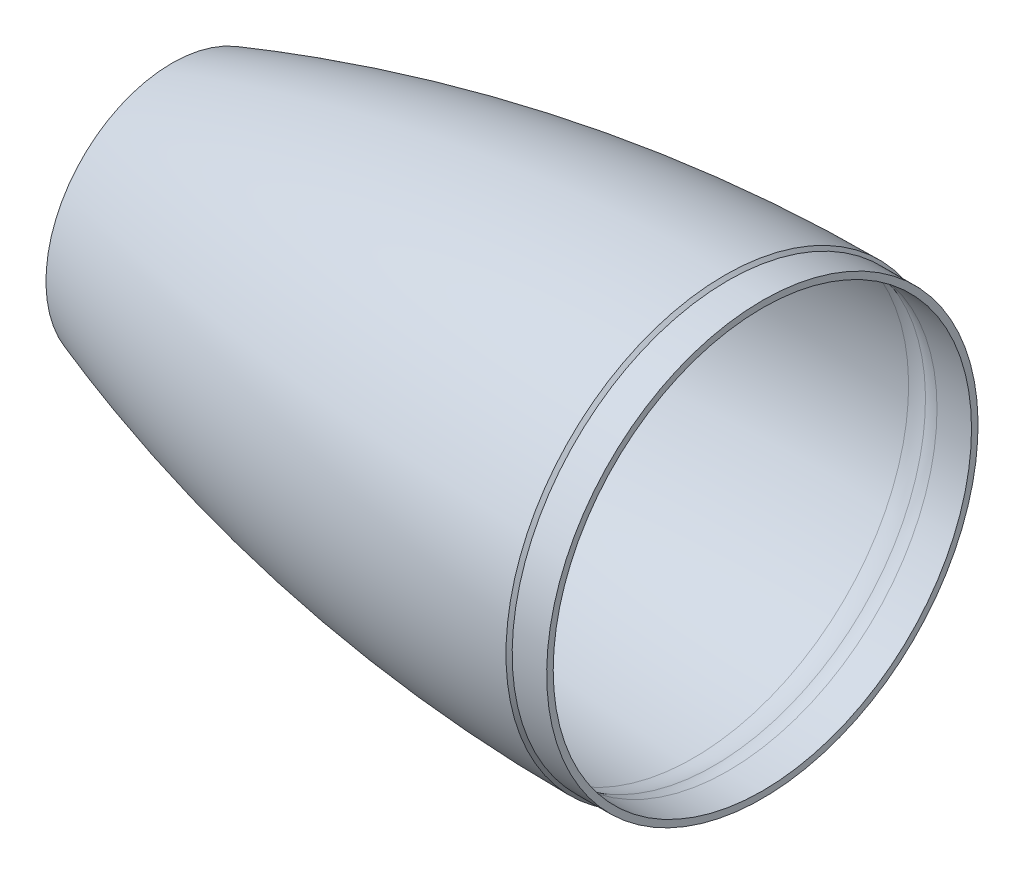
SolidWorks part; units mm, degrees
ref_plane "Front Plane" through (0, 0, 0) normal (0, 0, 1) x (1, 0, 0)
ref_plane "Top Plane" through (0, 0, 0) normal (0, 1, 0) x (1, 0, 0)
ref_plane "Right Plane" through (0, 0, 0) normal (1, 0, 0) x (0, 0, -1)
sketch "Sketch1" plane through (0, 0, 0) normal (0, 0, 1) x (1, 0, 0)
  line L4 (0, 0) -> (-304.8, 0) construction
  line L9 (0, 76.975) -> (0, 0) construction
  line L10 (0, 80.518) -> (50.8, 80.518) construction
  line L11 (-203.454, 46.355) -> (-203.454, 45.0852)
  line L15 (1.143, 79.375) -> (13.843, 79.375)
  line L16 (0, 80.518) -> (1.143, 79.375)
  line L17 (1.143, 76.975) -> (13.843, 76.975)
  line L18 (13.843, 76.975) -> (13.843, 79.375)
  arc A4 (0, 80.518) -> (-203.454, 46.355) centre (0, -542.3875) ccw
  arc A5 (-11.557, 79.2106) -> (-203.454, 45.0852) centre (0, -542.3875) ccw
  arc A6 (0, 79.318) -> (-203.0621, 45.2208) centre (0, -542.3875) ccw construction
  arc A10 (-4.0446, 77.9176) -> (1.143, 76.975) centre (1.143, 91.7214) ccw
  arc A13 (-11.557, 79.2106) -> (-4.0446, 77.9176) centre (-11.18, 58.9308) cw
  point P6 (-203.2, 45.0834)
  point P8 (-57.2734, -19.8104)
  point P9 (0, 313.4439)
  point P10 (-150.9565, 274.6984)
  point P12 (0, 0)
  dimension "D17" = 5.1876
  dimension "D16" = 12.7
  dimension "D1" = 161.036
  dimension "D2" = 50.8
  dimension "D3" = 203.454
  dimension "D4" = 92.71
  dimension "D9" = 304.8
  dimension "D12" = 12.7
  dimension "D13" = 158.75
  dimension "D14" = 45
  dimension "D15" = 2.4
  dimension "D5" = 1.2
revolve "Revolve1" add sketch "Sketch1" angle 360 about L4
